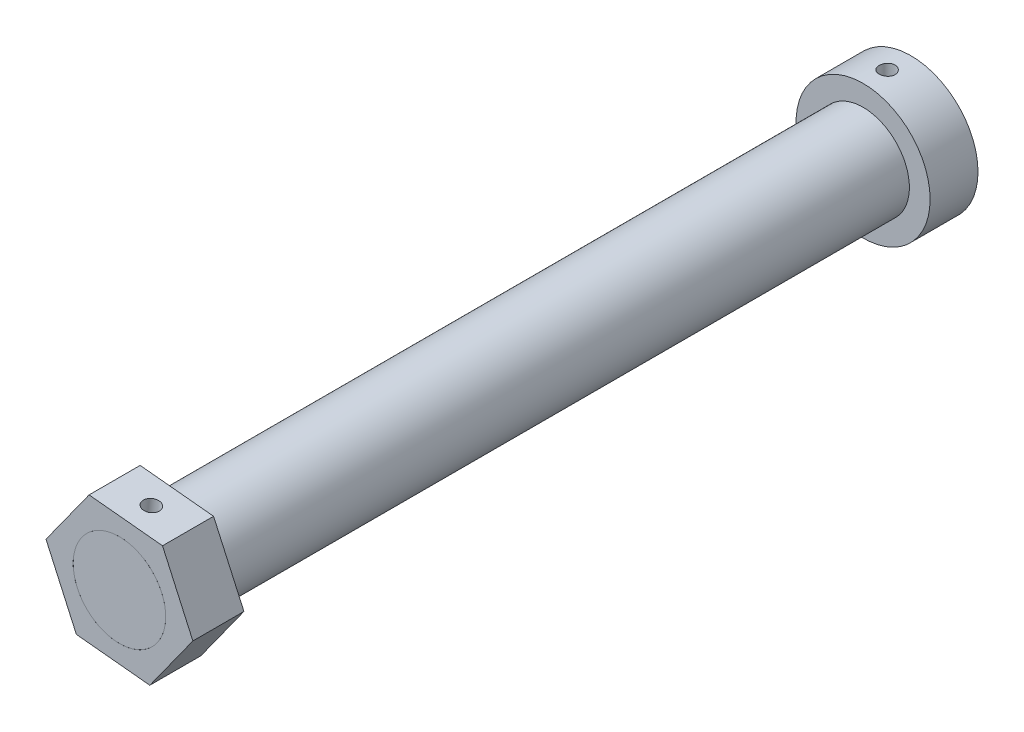
SolidWorks part; units mm, degrees
ref_plane "Front Plane" through (0, 0, 0) normal (0, 0, 1) x (1, 0, 0)
ref_plane "Top Plane" through (0, 0, 0) normal (0, 1, 0) x (1, 0, 0)
ref_plane "Right Plane" through (0, 0, 0) normal (1, 0, 0) x (0, 0, -1)
sketch "Sketch1" plane through (0, 0, 0) normal (0, 0, 1) x (1, 0, 0)
  circle A0 centre (0, 0) radius 21
  circle A1 centre (0, 0) radius 14.5
  dimension "D1" = 42
  dimension "D2" = 29
extrude "Boss-Extrude1" add sketch "Sketch1" along normal mid plane 15
sketch "Sketch2" plane through (0, 0, -7.5) normal (0, 0, -1) x (-1, 0, 0)
  circle A0 centre (0, 0) radius 14.5 construction
  circle A1 centre (0, 0) radius 14.5
extrude "Boss-Extrude2" add sketch "Sketch2" against normal blind 250 from offset 2 separate body
cosmetic thread "Cosmetic Thread1" parameters "D1"=210, "D2"=23.704
sketch "Sketch3" plane through (0, 0, 0) normal (0, 1, 0) x (1, 0, 0)
  circle A0 centre (0, 0) radius 2.5
  dimension "D1" = 5
extrude "Cut-Extrude1" cut sketch "Sketch3" against normal mid plane 115
sketch "Sketch4" plane through (0, 0, 240.5) normal (0, 0, 1) x (1, 0, 0)
  line L1 (13.4975, 18.7754) -> (-9.5112, 21.0769)
  line L2 (-9.5112, 21.0769) -> (-23.0087, 2.3015)
  line L3 (-23.0087, 2.3015) -> (-13.4975, -18.7754)
  line L4 (-13.4975, -18.7754) -> (9.5112, -21.0769)
  line L5 (9.5112, -21.0769) -> (23.0087, -2.3015)
  line L6 (23.0087, -2.3015) -> (13.4975, 18.7754)
  circle A0 centre (0, 0) radius 20.0256 construction
  circle A1 centre (0, 0) radius 14.5 construction
  circle A2 centre (0, 0) radius 14.5
extrude "Boss-Extrude3" add sketch "Sketch4" against normal blind 16 separate body
sketch "Sketch5" plane through (1.9932, 19.9261, 0) normal (0.0995, 0.995, 0) x (0.995, -0.0995, 0)
  circle A0 centre (0, -232.5) radius 2.5
extrude "Cut-Extrude2" cut sketch "Sketch5" against normal blind 47
